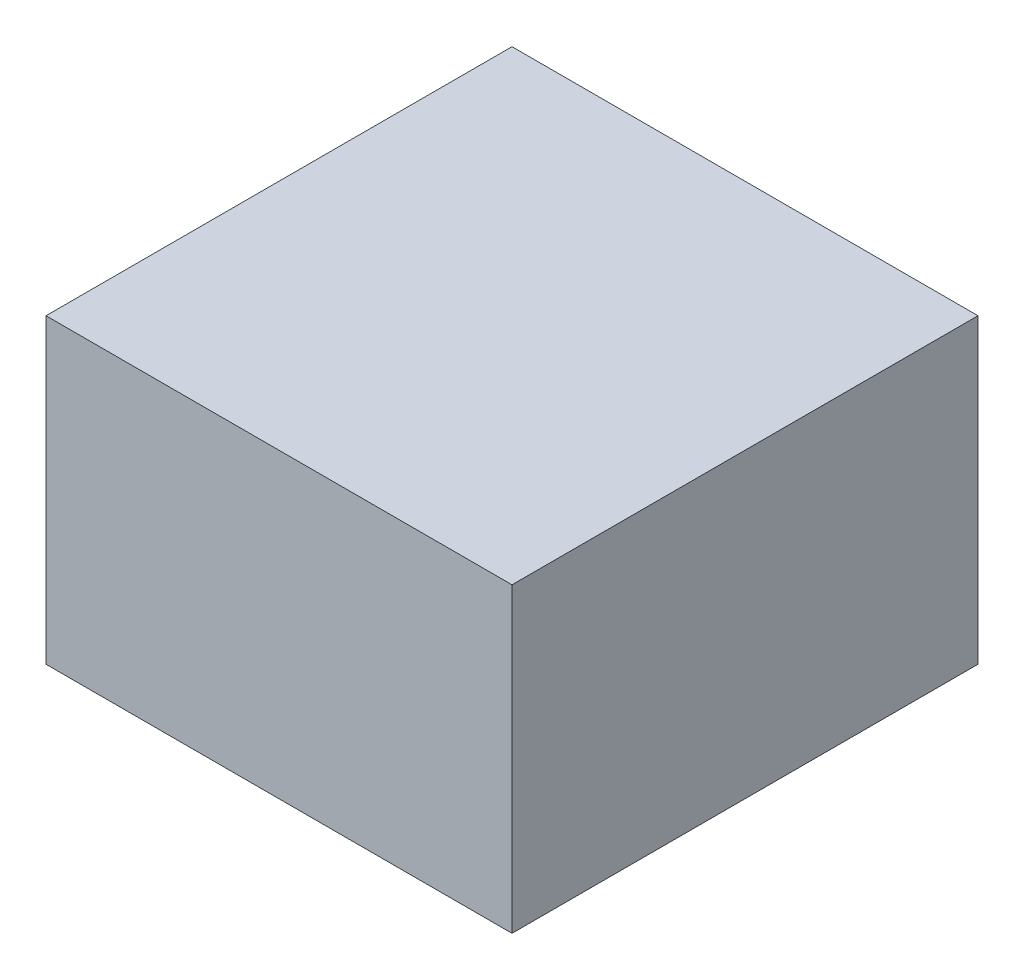
SolidWorks part; units mm, degrees
ref_plane "Front Plane" through (0, 0, 0) normal (0, 0, 1) x (1, 0, 0)
ref_plane "Top Plane" through (0, 0, 0) normal (0, 1, 0) x (1, 0, 0)
ref_plane "Right Plane" through (0, 0, 0) normal (1, 0, 0) x (0, 0, -1)
sketch "Sketch1" plane through (0, 0, 0) normal (0, 1, 0) x (1, 0, 0)
  line L1 (-0.88, 0.88) -> (0.88, 0.88)
  line L2 (-0.88, 0.88) -> (-0.88, -0.88)
  line L3 (-0.88, -0.88) -> (0.88, -0.88)
  line L4 (0.88, 0.88) -> (0.88, -0.88)
  line L5 (-0.88, 0.88) -> (0.88, -0.88) construction
  line L6 (-0.88, -0.88) -> (0.88, 0.88) construction
  point P0 (0, 0)
  dimension "D1" = 1.76
  dimension "D2" = 1.76
extrude "Boss-Extrude1" add sketch "Sketch1" along normal blind 1.14
